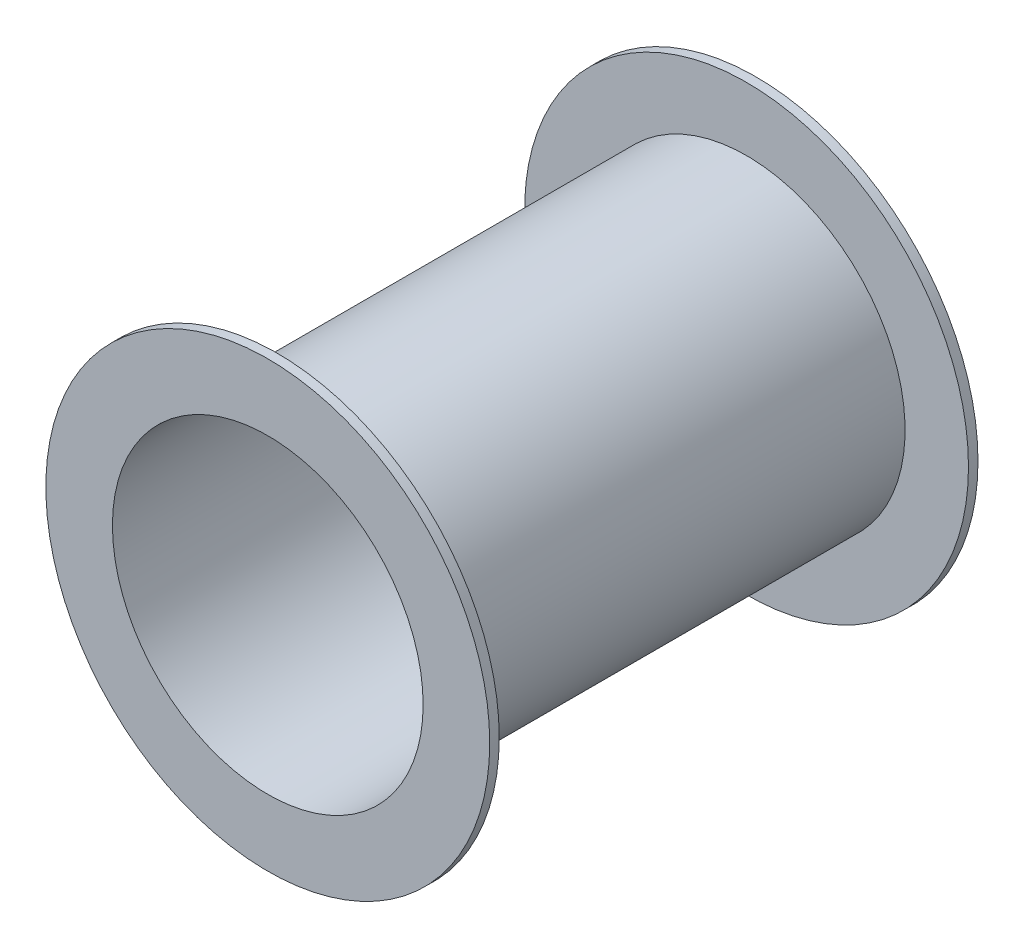
SolidWorks part; units mm, degrees
ref_plane "Front Plane" through (0, 0, 0) normal (0, 0, 1) x (1, 0, 0)
ref_plane "Top Plane" through (0, 0, 0) normal (0, 1, 0) x (1, 0, 0)
ref_plane "Right Plane" through (0, 0, 0) normal (1, 0, 0) x (0, 0, -1)
sketch "Sketch1" plane through (0, 0, 0) normal (0, 0, 1) x (1, 0, 0)
  circle A0 centre (0, 0) radius 100
  dimension "D1" = 200
extrude "Extrude-Thin1" add sketch "Sketch1" along normal blind 308 thin contours A0 thin type one direction reverse wall 2
sketch "Sketch2" plane through (0, 0, 308) normal (0, 0, 1) x (1, 0, 0)
  circle A0 centre (0, 0) radius 100 construction
  circle A1 centre (0, 0) radius 100
  circle A2 centre (0, 0) radius 140
  dimension "D1" = 280
extrude "Boss-Extrude1" add sketch "Sketch2" against normal blind 6
ref_plane "Plane1" through (0, 0, 154) normal (0, 0, -1) x (-1, 0, 0)
mirror "Mirror1" about plane through (0, 0, 154) normal (0, 0, -1) of "Boss-Extrude1", "Extrude-Thin1"
